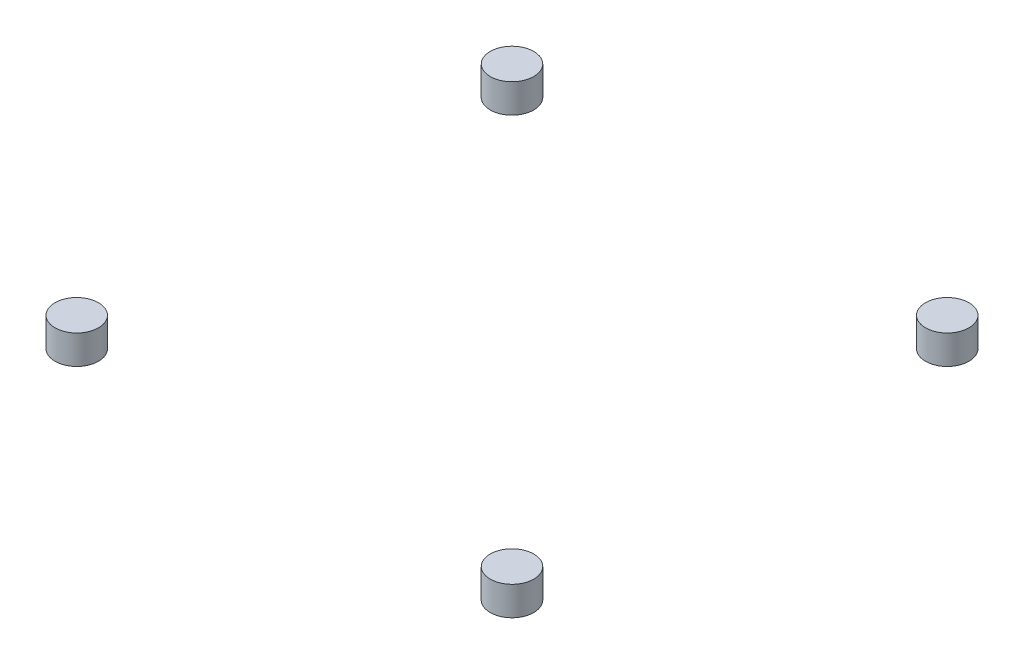
SolidWorks part; units mm, degrees
ref_plane "Front" through (0, 0, 0) normal (0, 0, 1) x (1, 0, 0)
ref_plane "Top" through (0, 0, 0) normal (0, 1, 0) x (1, 0, 0)
ref_plane "Right" through (0, 0, 0) normal (1, 0, 0) x (0, 0, -1)
sketch "Sketch1" plane through (0, 0, 0) normal (0, 1, 0) x (1, 0, 0)
  line L1 (0, 0) -> (150, 0) construction
  line L2 (0, 0) -> (0, 150) construction
  line L3 (0, 150) -> (150, 150) construction
  line L4 (150, 0) -> (150, 150) construction
  circle A0 centre (0, 150) radius 7.5
  circle A1 centre (150, 150) radius 7.5
  circle A2 centre (150, 0) radius 7.5
  circle A3 centre (0, 0) radius 7.5
  dimension "D3" = 15
  dimension "D1" = 150
  dimension "D2" = 150
extrude "Boss-Extrude1" add sketch "Sketch1" along normal blind 10
